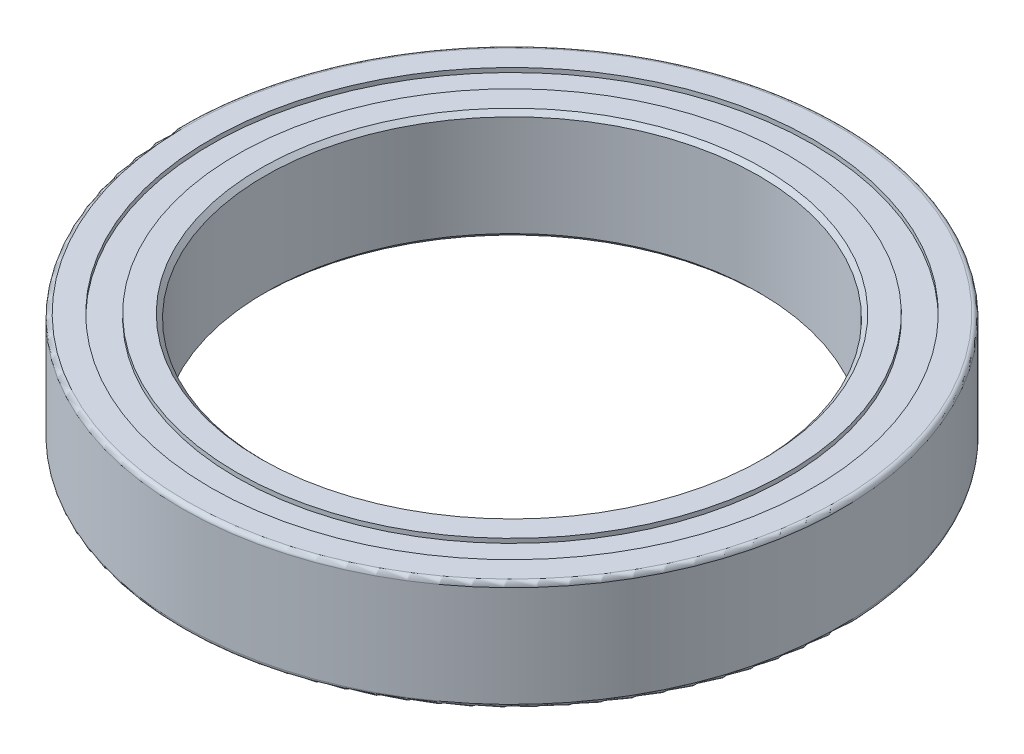
SolidWorks part; units mm, degrees
ref_plane "Front Plane" through (0, 0, 0) normal (0, 0, 1) x (1, 0, 0)
ref_plane "Top Plane" through (0, 0, 0) normal (0, 1, 0) x (1, 0, 0)
ref_plane "Right Plane" through (0, 0, 0) normal (1, 0, 0) x (0, 0, -1)
sketch "Sketch1" plane through (0, 0, 0) normal (0, 1, 0) x (1, 0, 0)
  circle A0 centre (0, 0) radius 7.1437
  circle A1 centre (0, 0) radius 7.9566
  circle A2 centre (0, 0) radius 9.525
  circle A3 centre (0, 0) radius 8.7122
  dimension "D1" = 14.2875
  dimension "D3" = 19.05
  dimension "D2" = 0.8128
  dimension "D4" = 0.8128
extrude "Boss-Extrude1" add sketch "Sketch1" along normal mid plane 3.175 contours A2 A3 | A1 A0
fillet "Fillet1" radius 0.127 2 edges at (0, -1.5875, 9.525) (0, 1.5875, 9.525)
chamfer "Chamfer1" distance 0.127 2 edges at (0, -1.5875, 7.1437) (0, 1.5875, 7.1437)
sketch "Sketch2" plane through (0, 0, 0) normal (0, 1, 0) x (1, 0, 0)
  circle A0 centre (0, 0) radius 8.7122 construction
  circle A1 centre (0, 0) radius 7.9566 construction
  circle A7 centre (0, 0) radius 7.9566
  circle A8 centre (0, 0) radius 8.7122
extrude "Boss-Extrude2" add sketch "Sketch2" along normal mid plane 2.921
equation "\"D1@Boss-Extrude2\"= \"D1@Boss-Extrude1\" - 0.01in"
